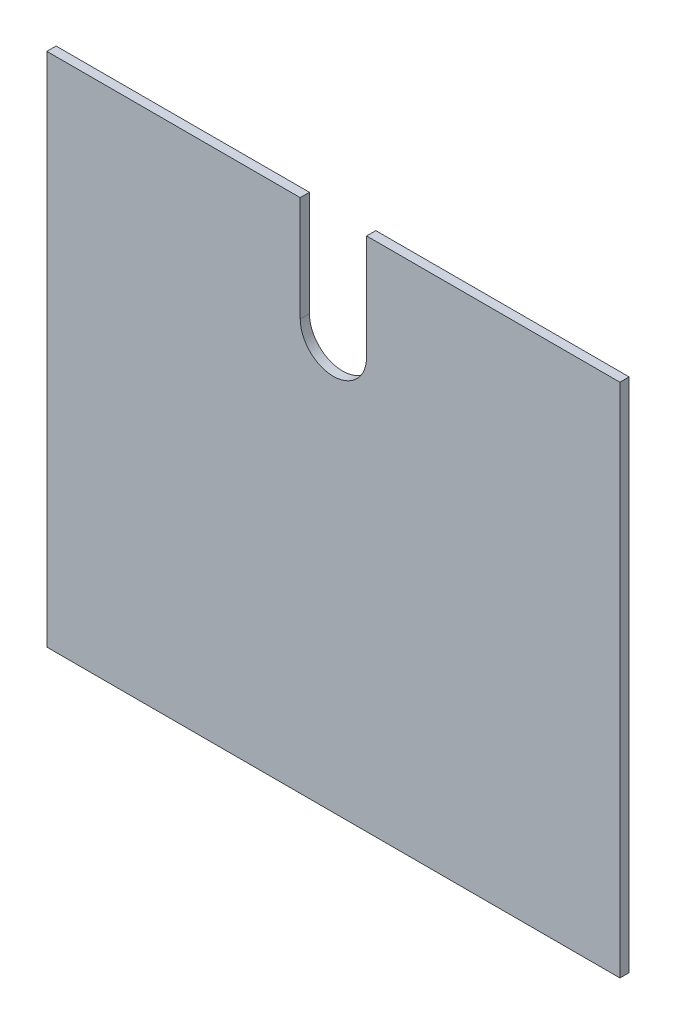
SolidWorks part; units mm, degrees
ref_plane "Front Plane" through (0, 0, 0) normal (0, 0, 1) x (1, 0, 0)
ref_plane "Top Plane" through (0, 0, 0) normal (0, 1, 0) x (1, 0, 0)
ref_plane "Right Plane" through (0, 0, 0) normal (1, 0, 0) x (0, 0, -1)
sketch "Sketch1" plane through (0, 0, 0) normal (0, 0, 1) x (1, 0, 0)
  line L0 (174.625, 355.6) -> (174.625, 283.21)
  line L1 (0, 0) -> (394.97, 0)
  line L2 (0, 0) -> (0, 355.6)
  line L3 (0, 355.6) -> (174.625, 355.6)
  line L4 (394.97, 0) -> (394.97, 355.6)
  line L5 (220.345, 355.6) -> (394.97, 355.6)
  line L6 (220.345, 283.21) -> (220.345, 355.6)
  line L7 (197.485, -49.3851) -> (197.485, 442.4543) construction
  arc A0 (174.625, 283.21) -> (220.345, 283.21) centre (197.485, 283.21) ccw
  point P12 (0, 0)
  dimension "D3" = 22.86
  dimension "D1" = 394.97
  dimension "D2" = 355.6
  dimension "D4" = 72.39
extrude "Boss-Extrude1" add sketch "Sketch1" along normal blind 6.35
ref_plane "Plane1" through (197.485, 0, 0) normal (-1, 0, 0) x (0, 0, 1)
